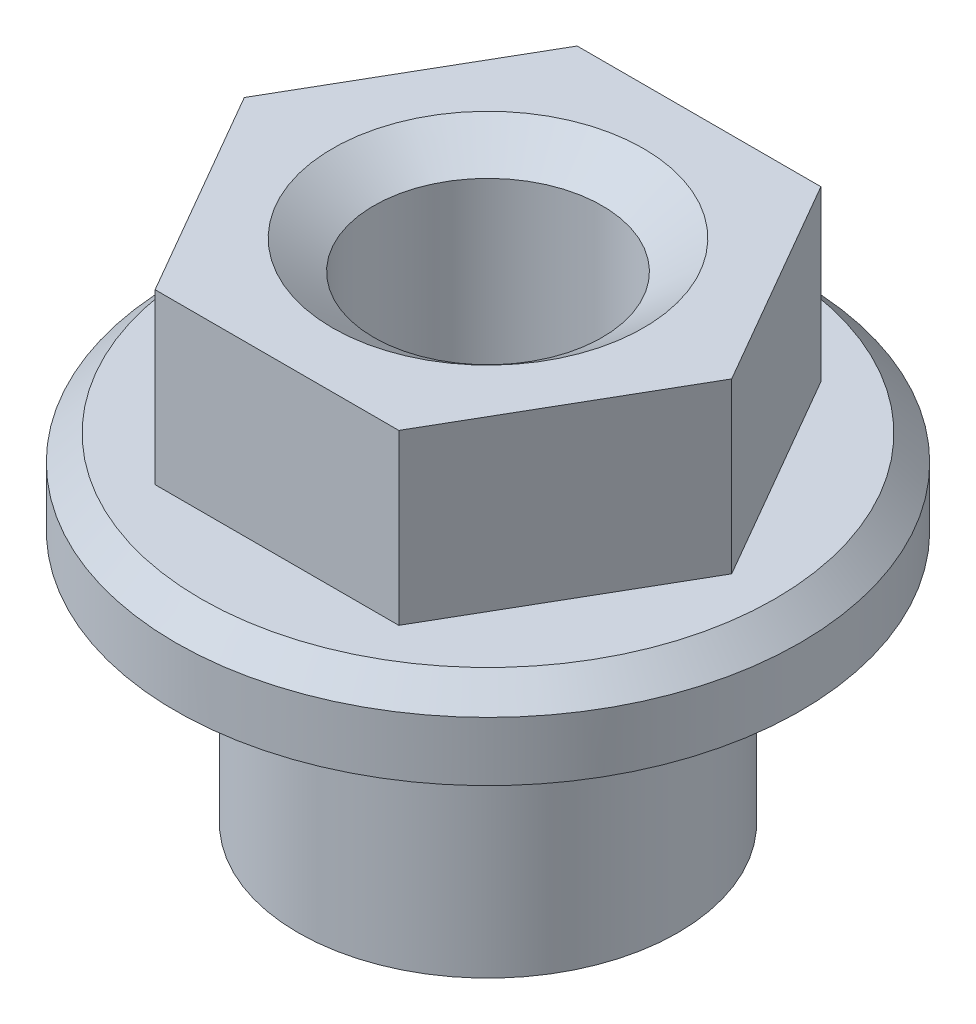
SolidWorks part; units mm, degrees
ref_plane "Спереди" through (0, 0, 0) normal (0, 0, 1) x (1, 0, 0)
ref_plane "Сверху" through (0, 0, 0) normal (0, 1, 0) x (1, 0, 0)
ref_plane "Справа" through (0, 0, 0) normal (1, 0, 0) x (0, 0, -1)
sketch "Эскиз1" plane through (0, 0, 0) normal (0, 0, 1) x (1, 0, 0)
  line L0 (0, 0) -> (0, 34.1614) construction
  line L1 (0, 0) -> (-2.25, 0)
  line L3 (-2.25, 0) -> (-2.25, 3)
  line L4 (-2.25, 3) -> (-3.7, 3)
  line L5 (-3.7, 3) -> (-3.7, 6)
  line L6 (-3.7, 6) -> (0, 6)
  line L8 (0, 6) -> (0, 0)
  dimension "D2" = 4.5
  dimension "D7" = 7.4
  dimension "D8" = 3
  dimension "D9" = 6
revolve "Повернуть1" add sketch "Эскиз1" angle 360 about L0
hole_wizard "Отверстие обработанное метчиком #6-321" positions "Эскиз4" profile "Эскиз3" tap size "#6-32" standard "Ansi (в дюймах)" end condition through all
sketch "Эскиз4" plane through (0, 6, 0) normal (0, 1, 0) x (-1, 0, 0)
  point P1 (0, 0)
sketch "Эскиз3" plane through (0, 6, 0) normal (1, 0, 0) x (0, 0, 1)
  line L0 (0, 0) -> (0, 6)
  line L1 (0, 6) -> (1.8415, 6)
  line L2 (1.3525, 5.6576) -> (1.3525, 0.3424)
  line L3 (1.3525, 0.3424) -> (1.8415, 0)
  line L5 (1.8415, 0) -> (0, 0)
  line L6 (-1.3525, 0.3424) -> (-1.8415, 0) construction
  line L7 (1.8415, 6) -> (1.3525, 5.6576)
  line L8 (-1.8415, 6) -> (-1.3526, 5.6576) construction
  line L11 (0, -6.35) -> (0, 107.95) construction
  dimension "Диаметр резьбы" = 2.7051
  dimension "Глубина проходного сверла" = 6
  dimension "Диаметр передней зенковки" = 3.683
  dimension "Угол передней зенковки" = 110
  dimension "Диаметр задней зенковки" = 3.683
  dimension "Угол задней зенковки" = 110
hole_wizard "Диаметр отверстия Ø1.0 (1)1" positions "Эскиз6" profile "Эскиз5" hole size "Ø1.0" standard "DIN"
sketch "Эскиз6" plane through (0, 5, 0) normal (0, 1, 0) x (-1, 0, 0)
  point P0 (-2.5, 0)
  point P1 (2.5, 0)
  dimension "D1" = 2.5
  dimension "D2" = 5
sketch "Эскиз5" plane through (2.5, 5, 0) normal (1, 0, 0) x (0, 0, 1)
  line L0 (0, 0) -> (0, 1.9504)
  line L1 (0, 1.9504) -> (0.5, 1.65)
  line L2 (0.5, 1.65) -> (0.5, 0)
  line L5 (0.5, 0) -> (0, 0)
  line L10 (0, 1.9504) -> (-0.5, 1.65) construction
  line L11 (0, -6.35) -> (0, 107.95) construction
  dimension "Диаметр отверстия" = 1
  dimension "Глубина отверстия" = 1.65
  dimension "Угол заточки сверла" = 118
sketch "Эскиз7" plane through (0, 6, 0) normal (0, 1, 0) x (1, 0, 0)
  line L1 (2.8868, 0) -> (1.4434, 2.5)
  line L2 (1.4434, 2.5) -> (-1.4434, 2.5)
  line L3 (-1.4434, 2.5) -> (-2.8868, 0)
  line L4 (-2.8868, 0) -> (-1.4434, -2.5)
  line L5 (-1.4434, -2.5) -> (1.4434, -2.5)
  line L6 (1.4434, -2.5) -> (2.8868, 0)
  circle A0 centre (0, 0) radius 2.5 construction
  dimension "D1" = 5
extrude "Вырез-Вытянуть1" cut sketch "Эскиз7" against normal offset from surface (2 mm away) 1 flip side to cut up to face at (0, 3, -2.25)
chamfer "Фаска1" distance 0.3 angle 45 1 edges at (0, 4, 3.7)
